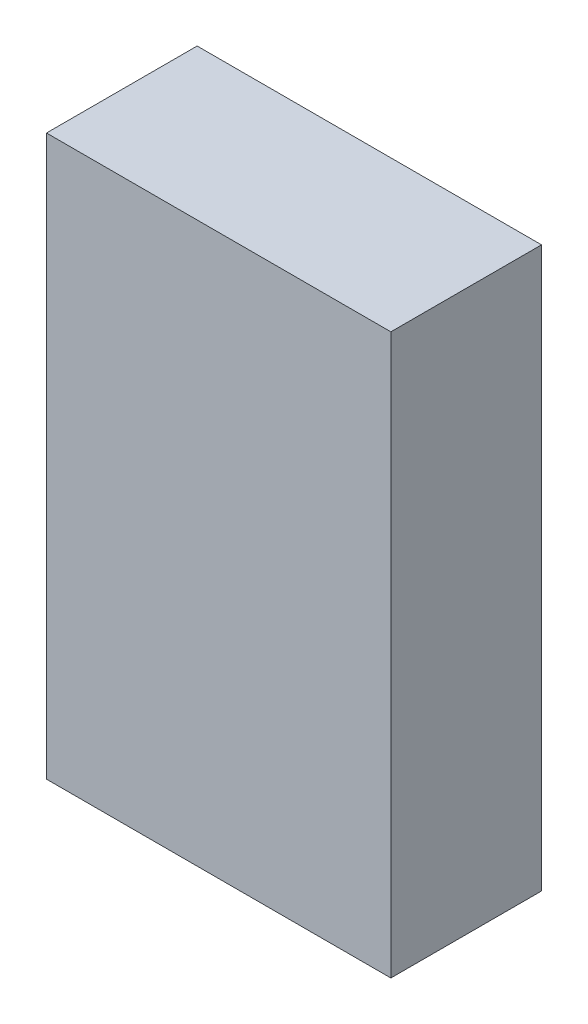
SolidWorks part; units mm, degrees
material "PET"
ref_plane "Front Plane" through (0, 0, 0) normal (0, 0, 1) x (1, 0, 0)
ref_plane "Top Plane" through (0, 0, 0) normal (0, 1, 0) x (1, 0, 0)
ref_plane "Right Plane" through (0, 0, 0) normal (1, 0, 0) x (0, 0, -1)
sketch "Sketch1" plane through (0, 0, 0) normal (0, 0, 1) x (1, 0, 0)
  line L0 (13.25, 23.7906) -> (13.25, 2.2094)
  line L1 (0, 0) -> (16, 0)
  line L2 (0, 0) -> (0, 26)
  line L3 (0, 26) -> (16, 26)
  line L4 (16, 0) -> (16, 26)
  line L5 (2.75, 23.7906) -> (2.75, 2.2094)
  line L6 (2.75, 13) -> (13.25, 13) construction
  arc A0 (2.75, 2.2094) -> (13.25, 2.2094) centre (8, 13) ccw
  arc A1 (13.25, 23.7906) -> (2.75, 23.7906) centre (8, 13) ccw
  point P6 (16, 13)
  point P13 (8, 13)
  point P14 (8, 0)
  dimension "D4" = 24
  dimension "D1" = 26
  dimension "D2" = 16
  dimension "D3" = 10.5
extrude "Boss-Extrude1" add sketch "Sketch1" along normal blind 3.5
sketch "Sketch2" plane through (0, 0, 3.5) normal (0, 0, 1) x (1, 0, 0)
  line L1 (0, 26) -> (16, 26)
  line L2 (0, 26) -> (0, 0)
  line L3 (0, 0) -> (16, 0)
  line L4 (16, 26) -> (16, 0)
extrude "Boss-Extrude2" add sketch "Sketch2" along normal blind 3.5
sketch "Sketch3" plane through (0, 0, 3.5) normal (0, 0, -1) x (-1, 0, 0)
  line L0 (0, 0) -> (-16, 0) construction
  line L1 (-16, 0) -> (-16, 26) construction
  circle A0 centre (-8, 13) radius 5
  point P4 (-8, 0)
  point P7 (-16, 13)
  dimension "D1" = 10
extrude "Cut-Extrude1" cut sketch "Sketch3" against normal blind 2.5
